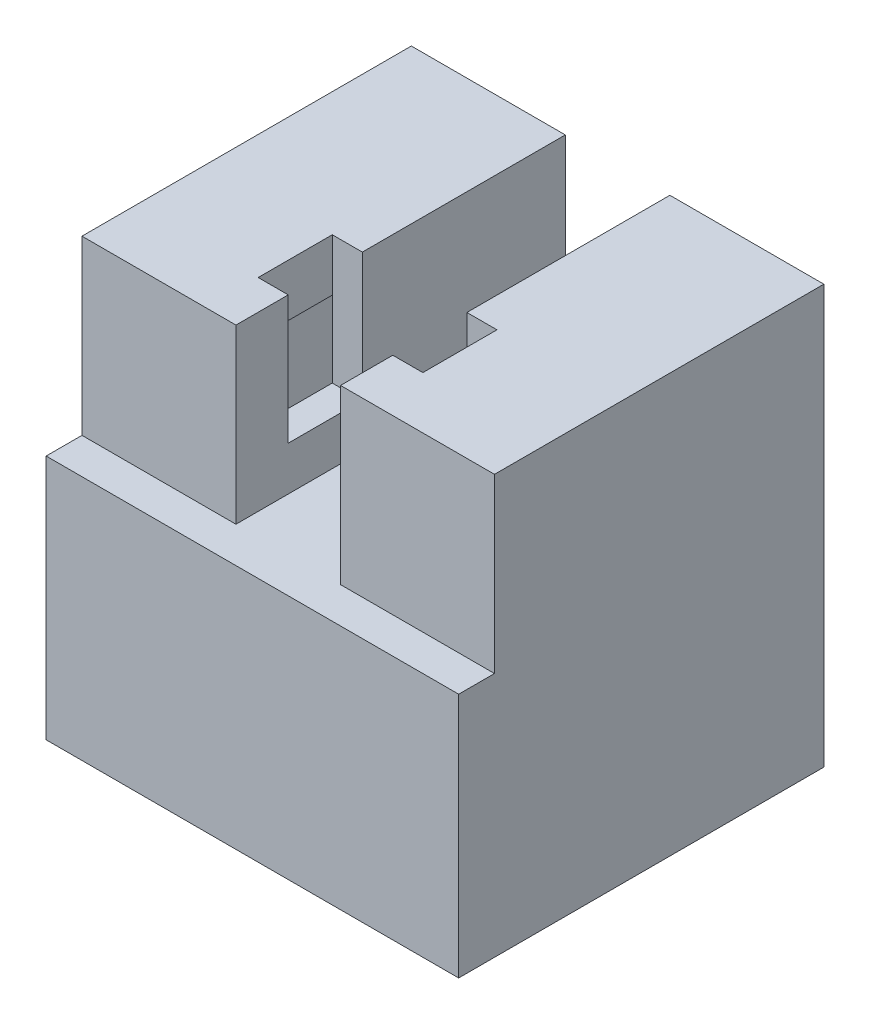
SolidWorks part; units mm, degrees
ref_plane "Front Plane" through (0, 0, 0) normal (0, 0, 1) x (1, 0, 0)
ref_plane "Top Plane" through (0, 0, 0) normal (0, 1, 0) x (1, 0, 0)
ref_plane "Right Plane" through (0, 0, 0) normal (1, 0, 0) x (0, 0, -1)
sketch "Sketch2" plane through (0, 0, 0) normal (0, 1, 0) x (1, 0, 0)
  line L1 (-9.35, 10) -> (9.35, 10)
  line L2 (-9.35, 10) -> (-9.35, -10)
  line L3 (-9.35, -10) -> (9.35, -10)
  line L4 (9.35, 10) -> (9.35, -10)
  point P4 (0, 10)
  point P6 (-9.35, 0)
  dimension "D1" = 18.7
  dimension "D2" = 20
extrude "Boss-Extrude1" add sketch "Sketch2" along normal blind 25.4
sketch "Sketch3" plane through (0, 0, -10) normal (0, 0, -1) x (-1, 0, 0)
  line L0 (-9.35, 25.4) -> (9.35, 25.4) construction
  line L1 (-3.175, 25.4) -> (3.175, 25.4)
  line L2 (-3.175, 25.4) -> (-3.175, 18.1)
  line L3 (-3.175, 18.1) -> (3.175, 18.1)
  line L4 (3.175, 25.4) -> (3.175, 18.1)
  line L5 (-9.35, 22.225) -> (9.35, 22.225) construction
  line L6 (-9.35, 25.4) -> (-9.35, 0) construction
  line L7 (9.35, 25.4) -> (9.35, 0) construction
  line L9 (-3.175, 18.1) -> (3.175, 18.1)
  line L10 (-3.175, 18.1) -> (-3.175, 14.925)
  line L11 (-3.175, 14.925) -> (3.175, 14.925)
  line L12 (3.175, 18.1) -> (3.175, 14.925)
  point P6 (0, 18.1)
  point P9 (6.0716, 19.725)
  line M12 (9.35, 25.4) -> (-9.35, 25.4)
  dimension "D1" = 6.35
  dimension "D2" = 3.175
  dimension "D3" = 2.5
  dimension "D4" = 1.625
  dimension "D5" = 3.175
extrude "Cut-Extrude1" cut sketch "Sketch3" against normal through all contours L12 L3 L10 L11 | L5 L2 L3 L4 | L2 L5 L4 M12
sketch "Sketch5" plane through (0, 0, -10) normal (0, 0, -1) x (-1, 0, 0)
  line L0 (9.35, 25.4) -> (9.35, 0) construction
  line L1 (-9.35, 25.4) -> (-12.525, 25.4)
  line L2 (-9.35, 25.4) -> (-9.35, 0)
  line L3 (-9.35, 0) -> (-12.525, 0)
  line L4 (-12.525, 25.4) -> (-12.525, 0)
  line L5 (9.35, 25.4) -> (12.525, 25.4)
  line L6 (9.35, 25.4) -> (9.35, 0)
  line L7 (9.35, 0) -> (12.525, 0)
  line L8 (12.525, 25.4) -> (12.525, 0)
  line L9 (-9.35, 0) -> (9.35, 0) construction
  dimension "D1" = 3.175
extrude "Boss-Extrude2" add sketch "Sketch5" against normal up to surface (20 mm away) up to face at (0, 16.4312, 10)
sketch "Sketch6" plane through (0, 0, -10) normal (0, 0, -1) x (-1, 0, 0)
  line L0 (-12.525, 0) -> (12.525, 0) construction
  line L1 (-9.35, 22.225) -> (-5, 22.225)
  line L2 (-9.35, 22.225) -> (-9.35, 0)
  line L3 (-9.35, 0) -> (-5, 0)
  line L4 (-5, 22.225) -> (-5, 0)
  line L5 (-3.175, 14.925) -> (3.175, 14.925) construction
  line L6 (-5, 10.125) -> (5, 10.125)
  line L7 (-5, 10.125) -> (-5, 0)
  line L8 (-5, 0) -> (5, 0)
  line L9 (5, 10.125) -> (5, 0)
  line L10 (9.35, 0) -> (5, 0)
  line L11 (9.35, 0) -> (9.35, 22.225)
  line L12 (9.35, 22.225) -> (5, 22.225)
  line L13 (5, 0) -> (5, 22.225)
  line L14 (-12.525, 25.4) -> (-3.175, 25.4) construction
  point P12 (0, 10.125)
  point P15 (0, 14.925)
  line M18 (-12.525, 0) -> (12.525, 0)
  dimension "D1" = 10
  dimension "D2" = 18.7
  dimension "D3" = 3.175
  dimension "D4" = 12.1
extrude "Cut-Extrude2" cut sketch "Sketch6" against normal blind 16.825 contours L13 L9 L11 L12 M18 | L9 L6 L4 M18 | L4 L1 L2 M18
sketch "Sketch7" plane through (5, 0, 0) normal (1, 0, 0) x (0, 0, -1)
  line L0 (-6.825, 22.225) -> (-6.825, 10.125) construction
  line L1 (-6.325, 21.475) -> (-3.325, 21.475)
  line L2 (-6.325, 21.475) -> (-6.325, 17.975)
  line L3 (-6.325, 17.975) -> (-3.325, 17.975)
  line L4 (-3.325, 21.475) -> (-3.325, 17.975)
  line L5 (-6.825, 22.225) -> (10, 22.225) construction
  point P6 (-4.825, 17.975)
  point P7 (-6.325, 19.725)
  dimension "D1" = 3
  dimension "D2" = 2
  dimension "D3" = 2.5
  dimension "D4" = 3.5
extrude "Cut-Extrude3" cut sketch "Sketch7" against normal up to surface (10 mm away) up to face at (-5, 16.175, -1.5875)
sketch "Sketch8" plane through (0, 0, -10) normal (0, 0, -1) x (-1, 0, 0)
  line L0 (9.35, 0) -> (12.525, 0) construction
  line L1 (-11, 10.125) -> (11, 10.125)
  line L2 (-11, 10.125) -> (-11, 0)
  line L3 (-11, 0) -> (11, 0)
  line L4 (11, 10.125) -> (11, 0)
  line L5 (-5, 10.125) -> (5, 10.125) construction
  point P9 (0, 10.125)
  dimension "D1" = 22
extrude "Cut-Extrude4" cut sketch "Sketch8" against normal blind 19
sketch "Sketch9" plane through (12.525, 0, 0) normal (1, 0, 0) x (0, 0, -1)
  line L0 (-10, 0) -> (-10, 25.4) construction
  line L1 (-10, 14.925) -> (-12.175, 14.925)
  line L2 (-10, 14.925) -> (-10, 0)
  line L3 (-10, 0) -> (-12.175, 0)
  line L4 (-12.175, 14.925) -> (-12.175, 0)
  line L5 (-10, 0) -> (10, 0) construction
  dimension "D1" = 3.175
extrude "Boss-Extrude3" add sketch "Sketch9" against normal up to surface (25.05 mm away) up to face at (-12.525, 12.7, 0)
ref_plane "Plane1" through (0, 0, 2.325) normal (0, 0, -1) x (-1, 0, 0)
sketch "Sketch10" plane through (0, 0, 2.325) normal (0, 0, -1) x (-1, 0, 0)
  line L0 (-5, 22.225) -> (-5, 10.125) construction
  line L1 (-5, 25.4) -> (-3.175, 25.4)
  line L2 (-5, 25.4) -> (-5, 17.6)
  line L3 (-5, 17.6) -> (-3.175, 17.6)
  line L4 (-3.175, 25.4) -> (-3.175, 17.6)
  line L5 (3.175, 25.4) -> (3.175, 14.925) construction
  line L6 (3.175, 25.4) -> (5, 25.4)
  line L7 (3.175, 25.4) -> (3.175, 17.6)
  line L8 (3.175, 17.6) -> (5, 17.6)
  line L9 (5, 25.4) -> (5, 17.6)
  line L10 (5, 10.125) -> (5, 22.225) construction
  line L11 (-12.525, 25.4) -> (-3.175, 25.4) construction
  line L12 (5, 10.125) -> (5, 22.225) construction
  line L13 (-3.175, 25.4) -> (-3.175, 14.925) construction
  line L14 (-3.175, 14.925) -> (3.175, 14.925) construction
  point P15 (-5, 25.4)
  point P18 (3.175, 25.4)
  point P20 (5, 16.5606)
  point P23 (3.175, 14.925)
  point P25 (-3.0352, 15.9461)
  point P26 (-3.175, 16.038)
  point P29 (0, 0)
  point P30 (3.175, 15.8459)
  point P31 (0, 0)
  dimension "D1" = 2.675
extrude "Cut-Extrude5" cut sketch "Sketch10" against normal up to surface (4.5 mm away) up to face at (-7.175, 16.175, 6.825)
